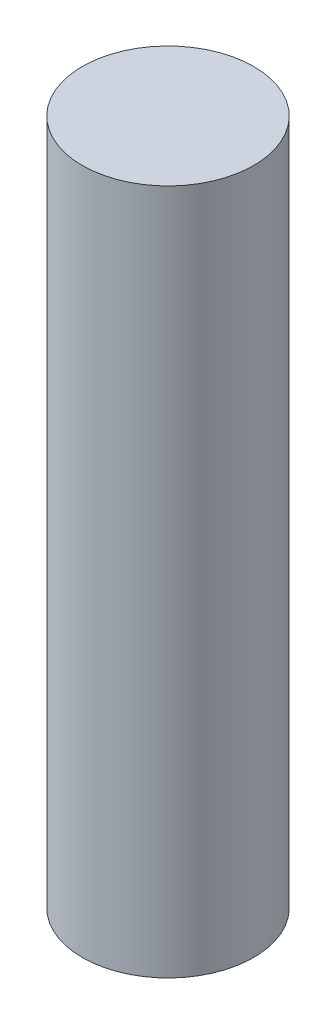
SolidWorks part; units mm, degrees
ref_plane "Front Plane" through (0, 0, 0) normal (0, 0, 1) x (1, 0, 0)
ref_plane "Top Plane" through (0, 0, 0) normal (0, 1, 0) x (1, 0, 0)
ref_plane "Right Plane" through (0, 0, 0) normal (1, 0, 0) x (0, 0, -1)
sketch "Sketch1" plane through (0, 0, 0) normal (0, 1, 0) x (1, 0, 0)
  circle A0 centre (0, 0) radius 15.875
  dimension "D1" = 31.75
extrude "Boss-Extrude1" add sketch "Sketch1" along normal blind 127
